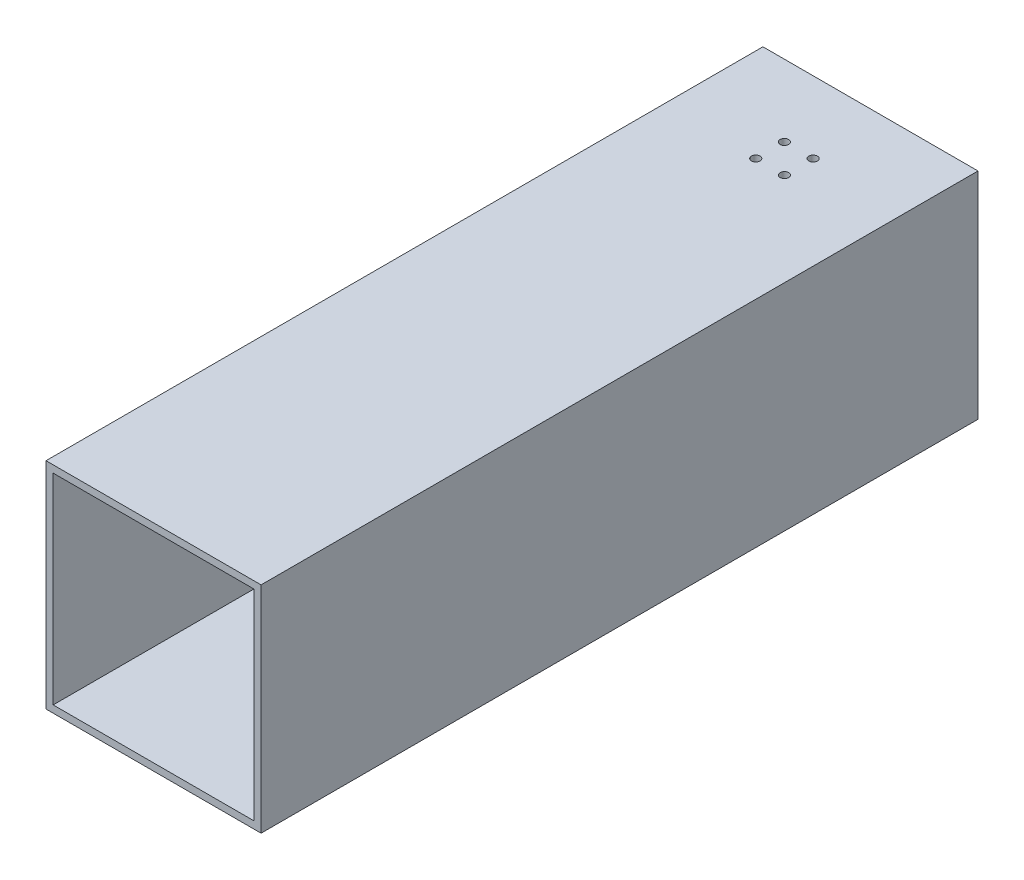
SolidWorks part; units mm, degrees
ref_plane "前视基准面" through (0, 0, 0) normal (0, 0, 1) x (1, 0, 0)
ref_plane "上视基准面" through (0, 0, 0) normal (0, 1, 0) x (1, 0, 0)
ref_plane "右视基准面" through (0, 0, 0) normal (1, 0, 0) x (0, 0, -1)
sketch "草图1" plane through (0, 0, 0) normal (0, 0, 1) x (1, 0, 0)
  line L1 (-75, -75) -> (75, -75)
  line L2 (-75, -75) -> (-75, 75)
  line L3 (-75, 75) -> (75, 75)
  line L4 (75, -75) -> (75, 75)
  line L5 (-75, -75) -> (75, 75) construction
  line L6 (-75, 75) -> (75, -75) construction
  point P0 (0, 0)
  dimension "D1" = 150
  dimension "D2" = 150
extrude "凸台-拉伸1" add sketch "草图1" along normal blind 500
sketch "草图2" plane through (0, 0, 500) normal (0, 0, 1) x (1, 0, 0)
  line L0 (75, 75) -> (-75, 75) construction
  line L1 (-70, -70) -> (70, -70)
  line L2 (-70, -70) -> (-70, 70)
  line L3 (-70, 70) -> (70, 70)
  line L4 (70, -70) -> (70, 70)
  line L5 (-70, -70) -> (70, 70) construction
  line L6 (-70, 70) -> (70, -70) construction
  line L7 (-75, 75) -> (-75, -75) construction
  point P0 (0, 0)
  dimension "D1" = 5
  dimension "D2" = 5
extrude "切除-拉伸1" cut sketch "草图2" against normal through all
sketch "草图3" plane through (0, 75, 0) normal (0, 1, 0) x (1, 0, 0)
  line L0 (75, 0) -> (-75, 0) construction
  point P0 (-10, -50)
  point P1 (10, -50)
  point P2 (10, -70)
  point P3 (-10, -70)
  dimension "D1" = 20
  dimension "D2" = 20
  dimension "D3" = 20
  dimension "D4" = 20
  dimension "D5" = 50
  dimension "D6" = 50
  dimension "D7" = 28.2843
  dimension "D8" = 10
hole_wizard "大小mm 暗销孔1" positions "草图4" profile "草图5" hole size "Ø6.0" standard "GB" end condition through all
sketch "草图4" plane through (0, 75, 0) normal (0, 1, 0) x (1, 0, 0)
  point P0 (-10, -50)
  point P3 (10, -50)
  point P6 (10, -70)
  point P9 (-10, -70)
sketch "草图5" plane through (-10, 75, 50) normal (1, 0, 0) x (0, 0, 1)
  line L0 (0, 0) -> (0, 150)
  line L1 (0, 150) -> (3, 150)
  line L2 (3, 150) -> (3, 0)
  line L5 (3, 0) -> (0, 0)
  line L11 (0, -6.35) -> (0, 107.95) construction
  dimension "通孔孔直径" = 6
  dimension "通孔孔深度" = 150
